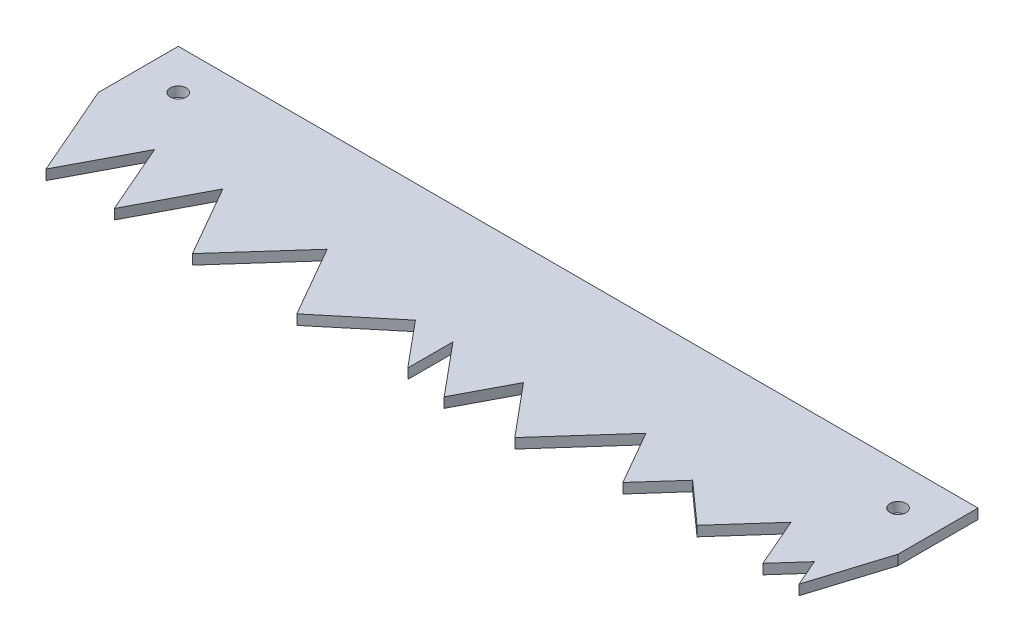
SolidWorks part; units mm, degrees
ref_plane "Front Plane" through (0, 0, 0) normal (0, 0, 1) x (1, 0, 0)
ref_plane "Top Plane" through (0, 0, 0) normal (0, 1, 0) x (1, 0, 0)
ref_plane "Right Plane" through (0, 0, 0) normal (1, 0, 0) x (0, 0, -1)
sketch "Sketch1" plane through (0, 0, 0) normal (0, 1, 0) x (1, 0, 0)
  line L1 (-127, 12.7) -> (127, 12.7)
  line L2 (-127, 12.7) -> (-127, -12.7)
  line L3 (-127, -12.7) -> (127, -12.7)
  line L4 (127, 12.7) -> (127, -12.7)
  line L5 (-127, 12.7) -> (127, -12.7) construction
  line L6 (-127, -12.7) -> (127, 12.7) construction
  point P4 (0, 0)
  dimension "D1" = 254
  dimension "D2" = 25.4
extrude "Boss-Extrude1" add sketch "Sketch1" along normal blind 3.175
sketch "Sketch2" plane through (0, 3.175, 0) normal (0, 1, 0) x (1, 0, 0)
  line L0 (-127, -12.7) -> (-114.2451, -42.0723)
  line L1 (-114.2451, -42.0723) -> (-102.3778, -19.4634)
  line L2 (-102.3778, -19.4634) -> (-92.5599, -42.0723)
  line L3 (-92.5599, -42.0723) -> (-80.6926, -19.4634)
  line L4 (-80.6926, -19.4634) -> (-67.7261, -42.0723)
  line L5 (-67.7261, -42.0723) -> (-47.5451, -19.4634)
  line L6 (-47.5451, -19.4634) -> (-34.5786, -42.0723)
  line L7 (-34.5786, -42.0723) -> (-14.0241, -24.9697)
  line L8 (-14.0241, -24.9697) -> (-2.0914, -39.3109)
  line L9 (-2.0914, -39.3109) -> (-2.0914, -24.9697)
  line L10 (-2.0914, -24.9697) -> (11.6495, -41.484)
  line L11 (11.6495, -41.484) -> (20.3177, -24.9697)
  line L12 (20.3177, -24.9697) -> (34.0586, -41.484)
  line L13 (34.0586, -41.484) -> (53.7145, -19.4634)
  line L14 (53.7145, -19.4634) -> (63.5836, -36.6715)
  line L15 (63.5836, -36.6715) -> (74.0287, -24.9697)
  line L16 (74.0287, -24.9697) -> (87.1383, -36.6715)
  line L17 (87.1383, -36.6715) -> (101.2107, -20.9061)
  line L18 (101.2107, -20.9061) -> (108.0569, -36.6715)
  line L19 (108.0569, -36.6715) -> (115.7647, -28.0364)
  line L20 (115.7647, -28.0364) -> (119.5145, -36.6715)
  line L21 (119.5145, -36.6715) -> (127, -12.7)
  line L22 (127, -12.7) -> (-127, -12.7)
extrude "Boss-Extrude2" add sketch "Sketch2" against normal blind 3.175
sketch "Sketch3" plane through (0, 3.175, 0) normal (0, 1, 0) x (1, 0, 0)
  line L0 (-127, 0) -> (127, 0) construction
  line L1 (-127, 12.7) -> (-127, -12.7) construction
  line L2 (127, -12.7) -> (127, 12.7) construction
  circle A0 centre (-114.3, 0) radius 2.54
  circle A1 centre (114.3, 0) radius 2.54
  dimension "D1" = 5.08
  dimension "D2" = 5.08
  dimension "D3" = 12.7
  dimension "D4" = 12.7
extrude "Cut-Extrude2" cut sketch "Sketch3" against normal through all
